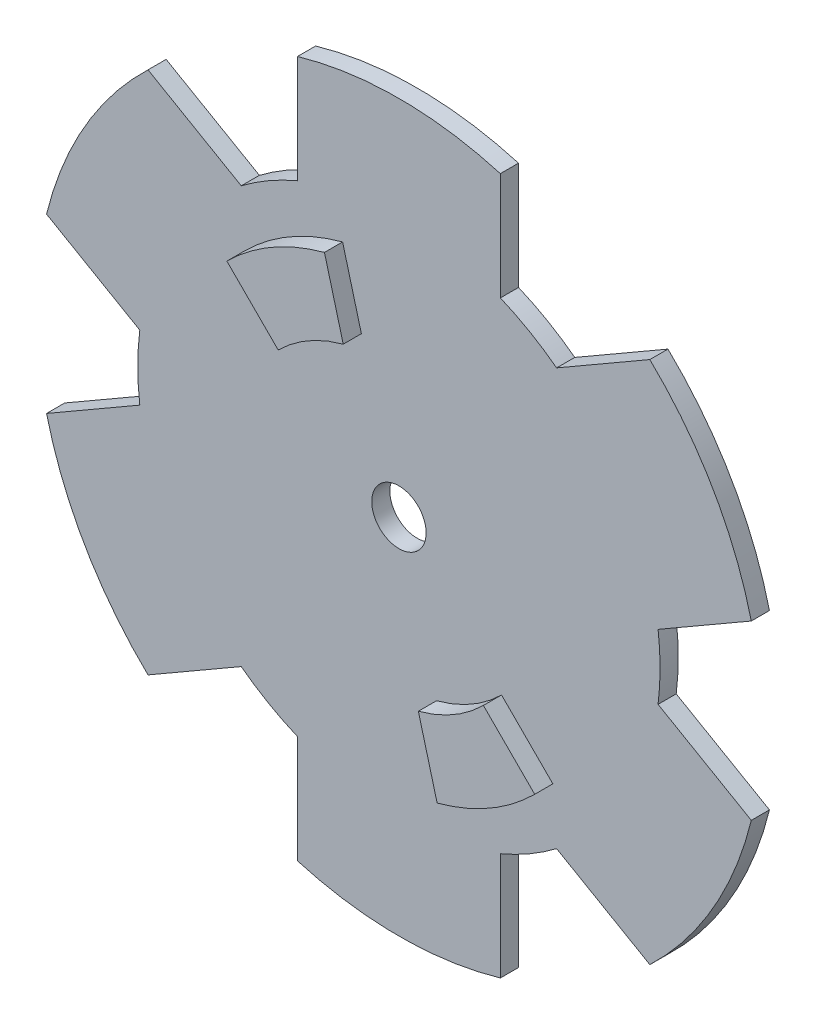
SolidWorks part; units mm, degrees
ref_plane "Front Plane" through (0, 0, 0) normal (0, 0, 1) x (1, 0, 0)
ref_plane "Top Plane" through (0, 0, 0) normal (0, 1, 0) x (1, 0, 0)
ref_plane "Right Plane" through (0, 0, 0) normal (1, 0, 0) x (0, 0, -1)
sketch "Sketch1" plane through (0, 0, 0) normal (0, 0, 1) x (1, 0, 0)
  line L15 (22.6794, 2.8416) -> (30.8387, 7.5524)
  line L16 (13.8006, 18.2201) -> (21.9599, 22.9309)
  line L17 (13.8006, -18.2201) -> (21.9599, -22.9309)
  line L18 (22.6794, -2.8416) -> (30.8387, -7.5524)
  line L19 (-8.8788, -21.0617) -> (-8.8788, -30.4833)
  line L20 (8.8788, -21.0617) -> (8.8788, -30.4833)
  line L21 (-22.6794, -2.8416) -> (-30.8387, -7.5524)
  line L22 (-13.8006, -18.2201) -> (-21.9599, -22.9309)
  line L23 (-13.8006, 18.2201) -> (-21.9599, 22.9309)
  line L24 (-22.6794, 2.8416) -> (-30.8387, 7.5524)
  line L40 (8.8788, 21.0617) -> (8.8788, 30.4833)
  line L41 (-8.8788, 21.0617) -> (-8.8788, 30.4833)
  line L54 (-8.8788, 30.4833) -> (-8.8788, 21.0617) construction
  arc A0 (-8.8788, 21.0617) -> (-13.8006, 18.2201) centre (0, 0) ccw construction
  arc A2 (8.8788, 30.4833) -> (-8.8788, 30.4833) centre (0, 0) ccw
  arc A3 (30.8387, 7.5524) -> (21.9599, 22.9309) centre (0, 0) ccw
  arc A4 (21.9599, -22.9309) -> (30.8387, -7.5524) centre (0, 0) ccw
  arc A6 (-8.8788, -30.4833) -> (8.8788, -30.4833) centre (0, 0) ccw
  arc A12 (-30.8387, -7.5524) -> (-21.9599, -22.9309) centre (0, 0) ccw
  arc A14 (-21.9599, 22.9309) -> (-30.8387, 7.5524) centre (0, 0) ccw
  arc A16 (8.8788, 21.0617) -> (13.8006, 18.2201) centre (0, 0) cw
  arc A18 (22.6794, 2.8416) -> (22.6794, -2.8416) centre (0, 0) cw
  arc A20 (13.8006, -18.2201) -> (8.8788, -21.0617) centre (0, 0) cw
  arc A22 (-8.8788, -21.0617) -> (-13.8006, -18.2201) centre (0, 0) cw
  arc A23 (-22.6794, -2.8416) -> (-22.6794, 2.8416) centre (0, 0) cw
  arc A44 (-13.8006, 18.2201) -> (-8.8788, 21.0617) centre (0, 0) cw
extrude "Extrude1" add sketch "Sketch1" along normal blind 1.5875
sketch "Sketch2" plane through (0, 0, 1.5875) normal (0, 0, 1) x (1, 0, 0)
  line L0 (0, 0) -> (0, 69.4182) construction
  line L1 (0, 0) -> (75, 0) construction
  line L2 (0, 0) -> (40.7467, 40.7467) construction
  circle A0 centre (0, 0) radius 2.3813
  dimension "D2" = 4.7625
  dimension "D1" = 45
extrude "Cut-Extrude1" cut sketch "Sketch2" against normal through all
sketch "Sketch3" plane through (0, 0, 1.5875) normal (0, 0, 1) x (1, 0, 0)
  line L0 (0, 0) -> (0, 36.1415) construction
  line L1 (0, 0) -> (52.3575, 0) construction
  line L2 (0, 0) -> (-24.0829, 41.7129) construction
  line L3 (0, 0) -> (-13.4704, 13.4704) construction
  line L4 (0, 0) -> (-4.9305, 18.4009) construction
  line L5 (0, 0) -> (32.7205, 18.8912) construction
  line L6 (0, 0) -> (-30.5221, -17.6219) construction
  line L7 (0, 0) -> (4.9305, -18.4009) construction
  line L8 (0, 0) -> (13.4704, -13.4704) construction
  line L9 (-13.4704, 13.4704) -> (-8.9803, 8.9803)
  line L10 (-4.9305, 18.4009) -> (-3.287, 12.2673)
  line L11 (13.4704, -13.4704) -> (8.9803, -8.9803)
  line L12 (4.9305, -18.4009) -> (3.287, -12.2673)
  circle A0 centre (0, 0) radius 12.7 construction
  circle A1 centre (0, 0) radius 19.05 construction
  arc A2 (-13.4704, 13.4704) -> (-4.9305, 18.4009) centre (0, 0) cw
  arc A3 (-8.9803, 8.9803) -> (-3.287, 12.2673) centre (0, 0) cw
  arc A4 (4.9305, -18.4009) -> (13.4704, -13.4704) centre (0, 0) ccw
  arc A5 (3.287, -12.2673) -> (8.9803, -8.9803) centre (0, 0) ccw
  dimension "D1" = 30
  dimension "D2" = 15
  dimension "D4" = 38.1
  dimension "D5" = 25.4
  dimension "D3" = 60
extrude "Boss-Extrude1" add sketch "Sketch3" along normal blind 1.5875
